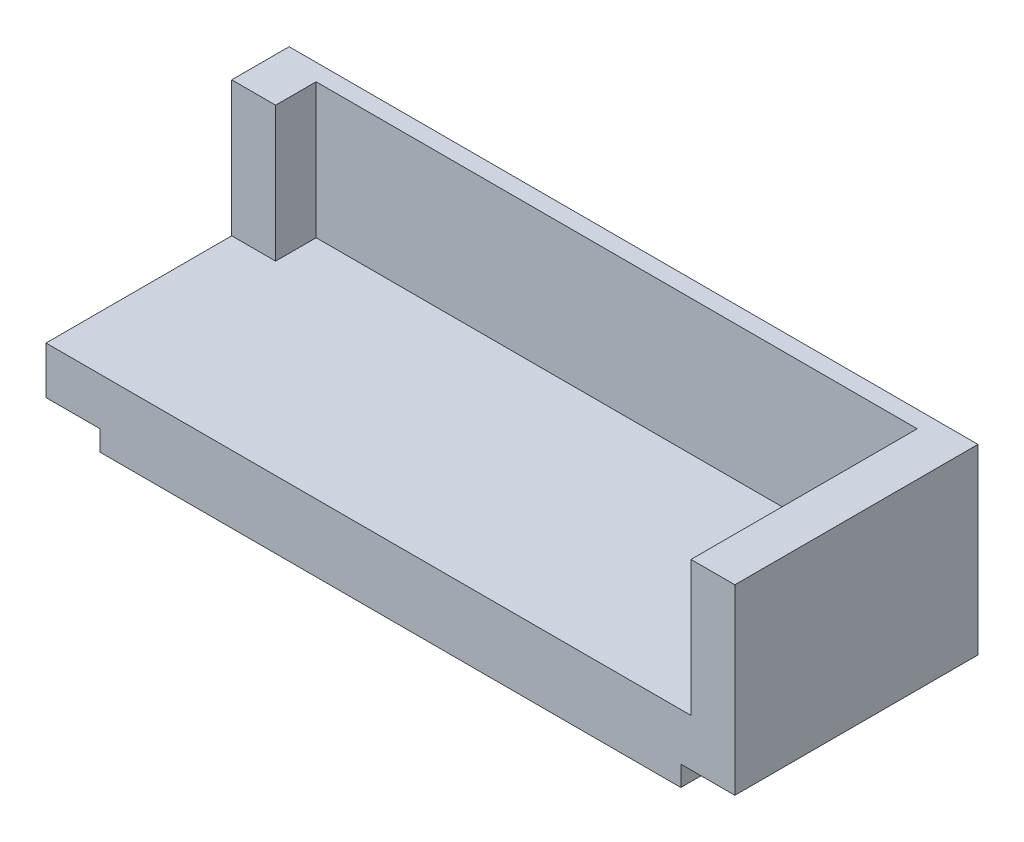
SolidWorks part; units mm, degrees
ref_plane "Plan de face" through (0, 0, 0) normal (0, 0, 1) x (1, 0, 0)
ref_plane "Plan de dessus" through (0, 0, 0) normal (0, 1, 0) x (1, 0, 0)
ref_plane "Plan de droite" through (0, 0, 0) normal (1, 0, 0) x (0, 0, -1)
sketch "Esquisse2" plane through (0, 0, 0) normal (0, 1, 0) x (1, 0, 0)
  line L1 (43, 18) -> (0, 18)
  line L2 (43, 18) -> (43, 0)
  line L3 (43, 0) -> (0, 0)
  line L4 (0, 18) -> (0, 0)
  dimension "D1" = 43
  dimension "D2" = 18
extrude "Boss.-Extru.1" add sketch "Esquisse2" along normal blind 3.5 and the other way blind 1.5
sketch "Esquisse3" plane through (43, 0, 0) normal (1, 0, 0) x (0, 0, -1)
  line L1 (0, 0) -> (18, 0)
  line L2 (0, 0) -> (0, 3.5)
  line L3 (0, 3.5) -> (18, 3.5)
  line L4 (18, 0) -> (18, 3.5)
sketch "Esquisse4" plane through (0, 0, 0) normal (-1, 0, 0) x (0, 0, 1)
  line L1 (0, 0) -> (-18, 0)
  line L2 (0, 0) -> (0, 3.5)
  line L3 (0, 3.5) -> (-18, 3.5)
  line L4 (-18, 0) -> (-18, 3.5)
extrude "Boss.-Extru.2" add sketch "Esquisse3" along normal blind 4
extrude "Boss.-Extru.3" add sketch "Esquisse4" along normal blind 4
sketch "Esquisse5" plane through (0, 3.5, 0) normal (0, 1, 0) x (1, 0, 0)
  line L0 (-4, 16.75) -> (47, 16.75) construction
  line L1 (-4, 0) -> (-4, 18) construction
  line L2 (47, 18) -> (47, 0) construction
  line L3 (47, 18) -> (-4, 18) construction
  line L5 (-4, 18) -> (47, 18)
  line L6 (-4, 18) -> (-4, 16.75)
  line L7 (-4, 16.75) -> (47, 16.75)
  line L8 (47, 18) -> (47, 16.75)
  dimension "D1" = 1.25
extrude "Boss.-Extru.4" add sketch "Esquisse5" along normal blind 10
sketch "Esquisse6" plane through (0, 3.5, 0) normal (0, 1, 0) x (1, 0, 0)
  line L0 (-4, 0) -> (47, 0) construction
  line L1 (47, 16.75) -> (43.75, 16.75)
  line L2 (47, 16.75) -> (47, 0)
  line L3 (47, 0) -> (43.75, 0)
  line L4 (43.75, 16.75) -> (43.75, 0)
  dimension "D1" = 3.25
extrude "Boss.-Extru.5" add sketch "Esquisse6" along normal blind 10
sketch "Esquisse7" plane through (0, 3.5, 0) normal (0, 1, 0) x (1, 0, 0)
  line L1 (-4, 16.75) -> (-0.75, 16.75)
  line L2 (-4, 16.75) -> (-4, 13.75)
  line L3 (-4, 13.75) -> (-0.75, 13.75)
  line L4 (-0.75, 16.75) -> (-0.75, 13.75)
  dimension "D1" = 3
  dimension "D2" = 3.25
extrude "Boss.-Extru.6" add sketch "Esquisse7" along normal blind 10
